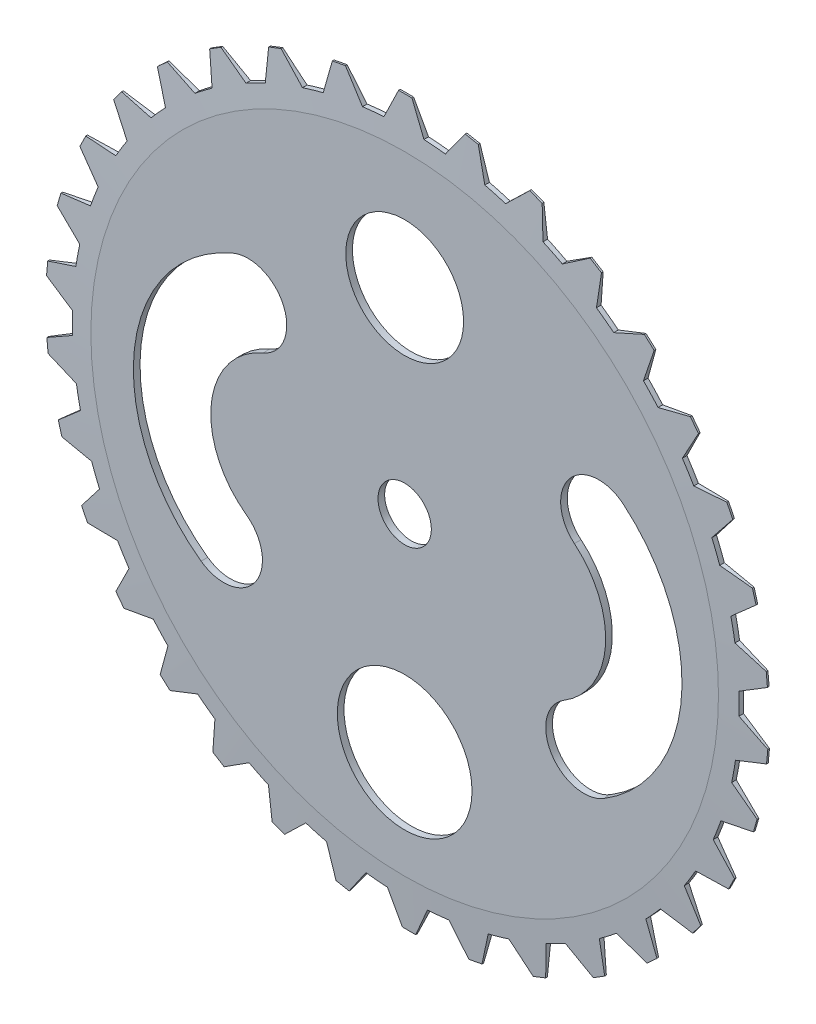
SolidWorks part; units mm, degrees
ref_plane "Front Plane" through (0, 0, 0) normal (0, 0, 1) x (1, 0, 0)
ref_plane "Top Plane" through (0, 0, 0) normal (0, 1, 0) x (1, 0, 0)
ref_plane "Right Plane" through (0, 0, 0) normal (1, 0, 0) x (0, 0, -1)
sketch "Sketch1" plane through (0, 0, 0) normal (0, 0, 1) x (1, 0, 0)
  circle A0 centre (0, 0) radius 63.5
  dimension "D1" = 127
extrude "Boss-Extrude1" add sketch "Sketch1" along normal blind 1.27 contours A0
sketch "Sketch2" plane through (0, 0, 1.27) normal (0, 0, 1) x (1, 0, 0)
  circle A0 centre (0, 0) radius 5.08
  dimension "D1" = 10.16
sketch "Sketch3" plane through (0, 0, 1.27) normal (0, 0, 1) x (1, 0, 0)
  circle A0 centre (0, 37.3308) radius 11.2182
  circle A1 centre (0, -39.311) radius 12.8285
  arc A2 (-29.8323, 19.8682) -> (-34.4638, -21.1959) centre (-20.5919, -1.9673) ccw construction
  arc A3 (-32.7056, 26.6578) -> (-38.7772, -27.175) centre (-20.5919, -1.9673) ccw
  arc A4 (-26.9591, 13.0785) -> (-30.1504, -15.2169) centre (-20.5919, -1.9673) ccw
  arc A5 (-26.9591, 13.0785) -> (-32.7056, 26.6578) centre (-29.8323, 19.8682) ccw
  arc A6 (-38.7772, -27.175) -> (-30.1504, -15.2169) centre (-34.4638, -21.1959) ccw
  arc A7 (36.9799, 16.8548) -> (34.1411, -21.7716) centre (21.7432, -1.4429) cw construction
  arc A8 (37.9274, -27.9799) -> (41.6332, 22.4428) centre (21.7432, -1.4429) ccw
  arc A9 (30.3548, -15.5633) -> (32.3267, 11.2667) centre (21.7432, -1.4429) ccw
  arc A10 (30.3548, -15.5633) -> (37.9274, -27.9799) centre (34.1411, -21.7716) ccw
  arc A11 (41.6332, 22.4428) -> (32.3267, 11.2667) centre (36.9799, 16.8548) ccw
  point P7 (-44.1527, 0.6901)
  point P12 (45.4901, -3.1882)
extrude "Cut-Extrude3" cut sketch "Sketch3" against normal blind 1.27
extrude "Cut-Extrude4" cut sketch "Sketch2" against normal blind 1.27
sketch "Sketch4" plane through (0, 0, 1.27) normal (0, 0, 1) x (1, 0, 0)
  line L0 (-4.1419, 63.3648) -> (3.4781, 63.4047)
  line L1 (-0.3573, 68.8319) -> (0.9127, 68.8319)
  line L2 (0.9127, 68.8319) -> (3.4781, 63.4047)
  line L3 (7.5719, 63.0469) -> (11.0482, 67.9589)
  line L4 (-4.1419, 63.3648) -> (-1.6273, 68.8319)
  line L5 (-1.6273, 68.8319) -> (-0.3573, 68.8319)
  line L6 (11.0482, 67.9589) -> (12.2966, 67.7255)
  line L7 (12.2966, 67.7255) -> (13.545, 67.4922)
  line L8 (13.545, 67.4922) -> (15.0695, 61.686)
  line L9 (7.5719, 63.0469) -> (15.0695, 61.686)
  line L10 (19.0278, 60.5821) -> (23.3475, 64.7717)
  line L11 (23.3475, 64.7717) -> (24.5318, 64.3129)
  line L12 (24.5318, 64.3129) -> (25.716, 63.8541)
  line L13 (25.716, 63.8541) -> (26.1477, 57.8667)
  line L14 (19.0278, 60.5821) -> (26.1477, 57.8667)
  line L15 (29.8358, 56.0542) -> (34.8517, 59.3787)
  line L16 (34.8517, 59.3787) -> (35.9315, 58.7101)
  line L17 (35.9315, 58.7101) -> (37.0113, 58.0416)
  line L18 (37.0113, 58.0416) -> (36.3354, 52.0767)
  line L19 (29.8358, 56.0542) -> (36.3354, 52.0767)
  line L20 (39.6277, 49.6175) -> (45.1691, 51.9637)
  line L21 (45.1691, 51.9637) -> (46.1077, 51.1081)
  line L22 (46.1077, 51.1081) -> (47.0462, 50.2525)
  line L23 (47.0462, 50.2525) -> (45.2858, 44.5134)
  line L24 (39.6277, 49.6175) -> (45.2858, 44.5134)
  line L25 (48.0701, 41.4911) -> (53.9483, 42.7791)
  line L26 (53.9483, 42.7791) -> (54.7137, 41.7656)
  line L27 (54.7137, 41.7656) -> (55.479, 40.7521)
  line L28 (55.479, 40.7521) -> (52.6941, 35.4343)
  line L29 (48.0701, 41.4911) -> (52.6941, 35.4343)
  line L30 (54.8756, 31.9518) -> (60.8904, 32.1377)
  line L31 (60.8904, 32.1377) -> (61.4565, 31.0008)
  line L32 (61.4565, 31.0008) -> (62.0226, 29.864)
  line L33 (62.0226, 29.864) -> (58.3079, 25.1484)
  line L34 (54.8756, 31.9518) -> (58.3079, 25.1484)
  line L35 (59.8124, 21.3244) -> (65.7589, 20.4019)
  line L36 (65.7589, 20.4019) -> (66.1065, 19.1804)
  line L37 (66.1065, 19.1804) -> (66.454, 17.9589)
  line L38 (66.454, 17.9589) -> (61.9361, 14.0062)
  line L39 (59.8124, 21.3244) -> (61.9361, 14.0062)
  line L40 (62.7123, 9.9708) -> (68.3881, 7.9714)
  line L41 (68.3881, 7.9714) -> (68.5053, 6.7068)
  line L42 (68.5053, 6.7068) -> (68.6225, 5.4422)
  line L43 (68.6225, 5.4422) -> (63.4551, 2.387)
  line L44 (62.7123, 9.9708) -> (63.4551, 2.387)
  line L45 (63.4766, -1.7223) -> (68.6884, -4.7306)
  line L46 (68.6884, -4.7306) -> (68.5712, -5.9952)
  line L47 (68.5712, -5.9952) -> (68.454, -7.2598)
  line L48 (68.454, -7.2598) -> (62.8133, -9.3135)
  line L49 (63.4766, -1.7223) -> (62.8133, -9.3135)
  line L50 (62.0793, -13.3568) -> (66.6496, -17.2715)
  line L51 (66.6496, -17.2715) -> (66.302, -18.4931)
  line L52 (66.302, -18.4931) -> (65.9545, -19.7146)
  line L53 (65.9545, -19.7146) -> (60.0324, -20.6969)
  line L54 (62.0793, -13.3568) -> (60.0324, -20.6969)
  line L55 (58.568, -24.5364) -> (62.3411, -29.2243)
  line L56 (62.3411, -29.2243) -> (61.775, -30.3612)
  line L57 (61.775, -30.3612) -> (61.2089, -31.498)
  line L58 (61.2089, -31.498) -> (55.2072, -31.3754)
  line L59 (58.568, -24.5364) -> (55.2072, -31.3754)
  line L60 (53.0622, -34.8805) -> (55.9097, -40.1818)
  line L61 (55.9097, -40.1818) -> (55.1443, -41.1953)
  line L62 (55.1443, -41.1953) -> (54.379, -42.2088)
  line L63 (54.379, -42.2088) -> (48.502, -40.9854)
  line L64 (53.0622, -34.8805) -> (48.502, -40.9854)
  line L65 (45.7495, -44.0368) -> (47.5743, -49.7711)
  line L66 (47.5743, -49.7711) -> (46.6358, -50.6266)
  line L67 (46.6358, -50.6266) -> (45.6972, -51.4822)
  line L68 (45.6972, -51.4822) -> (40.1451, -49.1998)
  line L69 (45.7495, -44.0368) -> (40.1451, -49.1998)
  line L70 (36.8788, -51.6934) -> (37.6189, -57.6654)
  line L71 (37.6189, -57.6654) -> (36.5391, -58.3339)
  line L72 (36.5391, -58.3339) -> (35.4593, -59.0025)
  line L73 (35.4593, -59.0025) -> (30.4211, -55.7387)
  line L74 (36.8788, -51.6934) -> (30.4211, -55.7387)
  line L75 (26.7522, -57.5897) -> (26.3824, -63.596)
  line L76 (26.3824, -63.596) -> (25.1981, -64.0547)
  line L77 (25.1981, -64.0547) -> (24.0139, -64.5135)
  line L78 (24.0139, -64.5135) -> (19.6612, -60.3795)
  line L79 (26.7522, -57.5897) -> (19.6612, -60.3795)
  line L80 (15.7146, -61.5248) -> (14.2474, -67.3609)
  line L81 (14.2474, -67.3609) -> (12.999, -67.5942)
  line L82 (12.999, -67.5942) -> (11.7507, -67.8276)
  line L83 (11.7507, -67.8276) -> (8.2317, -62.9642)
  line L84 (15.7146, -61.5248) -> (8.2317, -62.9642)
  line L85 (4.1419, -63.3648) -> (1.6273, -68.8319)
  line L86 (1.6273, -68.8319) -> (0.3573, -68.8319)
  line L87 (0.3573, -68.8319) -> (-0.9127, -68.8319)
  line L88 (-0.9127, -68.8319) -> (-3.4781, -63.4047)
  line L89 (4.1419, -63.3648) -> (-3.4781, -63.4047)
  line L90 (-7.5719, -63.0469) -> (-11.0482, -67.9589)
  line L91 (-11.0482, -67.9589) -> (-12.2966, -67.7255)
  line L92 (-12.2966, -67.7255) -> (-13.545, -67.4922)
  line L93 (-13.545, -67.4922) -> (-15.0695, -61.686)
  line L94 (-7.5719, -63.0469) -> (-15.0695, -61.686)
  line L95 (-19.0278, -60.5821) -> (-23.3475, -64.7717)
  line L96 (-23.3475, -64.7717) -> (-24.5318, -64.3129)
  line L97 (-24.5318, -64.3129) -> (-25.716, -63.8541)
  line L98 (-25.716, -63.8541) -> (-26.1477, -57.8667)
  line L99 (-19.0278, -60.5821) -> (-26.1477, -57.8667)
  line L100 (-29.8358, -56.0542) -> (-34.8517, -59.3787)
  line L101 (-34.8517, -59.3787) -> (-35.9315, -58.7101)
  line L102 (-35.9315, -58.7101) -> (-37.0113, -58.0416)
  line L103 (-37.0113, -58.0416) -> (-36.3354, -52.0767)
  line L104 (-29.8358, -56.0542) -> (-36.3354, -52.0767)
  line L105 (-39.6277, -49.6175) -> (-45.1691, -51.9637)
  line L106 (-45.1691, -51.9637) -> (-46.1077, -51.1081)
  line L107 (-46.1077, -51.1081) -> (-47.0462, -50.2525)
  line L108 (-47.0462, -50.2525) -> (-45.2858, -44.5134)
  line L109 (-39.6277, -49.6175) -> (-45.2858, -44.5134)
  line L110 (-48.0701, -41.4911) -> (-53.9483, -42.7791)
  line L111 (-53.9483, -42.7791) -> (-54.7137, -41.7656)
  line L112 (-54.7137, -41.7656) -> (-55.479, -40.7521)
  line L113 (-55.479, -40.7521) -> (-52.6941, -35.4343)
  line L114 (-48.0701, -41.4911) -> (-52.6941, -35.4343)
  line L115 (-54.8756, -31.9518) -> (-60.8904, -32.1377)
  line L116 (-60.8904, -32.1377) -> (-61.4565, -31.0008)
  line L117 (-61.4565, -31.0008) -> (-62.0226, -29.864)
  line L118 (-62.0226, -29.864) -> (-58.3079, -25.1484)
  line L119 (-54.8756, -31.9518) -> (-58.3079, -25.1484)
  line L120 (-59.8124, -21.3244) -> (-65.7589, -20.4019)
  line L121 (-65.7589, -20.4019) -> (-66.1065, -19.1804)
  line L122 (-66.1065, -19.1804) -> (-66.454, -17.9589)
  line L123 (-66.454, -17.9589) -> (-61.9361, -14.0062)
  line L124 (-59.8124, -21.3244) -> (-61.9361, -14.0062)
  line L125 (-62.7123, -9.9708) -> (-68.3881, -7.9714)
  line L126 (-68.3881, -7.9714) -> (-68.5053, -6.7068)
  line L127 (-68.5053, -6.7068) -> (-68.6225, -5.4422)
  line L128 (-68.6225, -5.4422) -> (-63.4551, -2.387)
  line L129 (-62.7123, -9.9708) -> (-63.4551, -2.387)
  line L130 (-63.4766, 1.7223) -> (-68.6884, 4.7306)
  line L131 (-68.6884, 4.7306) -> (-68.5712, 5.9952)
  line L132 (-68.5712, 5.9952) -> (-68.454, 7.2598)
  line L133 (-68.454, 7.2598) -> (-62.8133, 9.3135)
  line L134 (-63.4766, 1.7223) -> (-62.8133, 9.3135)
  line L135 (-62.0793, 13.3568) -> (-66.6496, 17.2715)
  line L136 (-66.6496, 17.2715) -> (-66.302, 18.4931)
  line L137 (-66.302, 18.4931) -> (-65.9545, 19.7146)
  line L138 (-65.9545, 19.7146) -> (-60.0324, 20.6969)
  line L139 (-62.0793, 13.3568) -> (-60.0324, 20.6969)
  line L140 (-58.568, 24.5364) -> (-62.3411, 29.2243)
  line L141 (-62.3411, 29.2243) -> (-61.775, 30.3612)
  line L142 (-61.775, 30.3612) -> (-61.2089, 31.498)
  line L143 (-61.2089, 31.498) -> (-55.2072, 31.3754)
  line L144 (-58.568, 24.5364) -> (-55.2072, 31.3754)
  line L145 (-53.0622, 34.8805) -> (-55.9097, 40.1818)
  line L146 (-55.9097, 40.1818) -> (-55.1443, 41.1953)
  line L147 (-55.1443, 41.1953) -> (-54.379, 42.2088)
  line L148 (-54.379, 42.2088) -> (-48.502, 40.9854)
  line L149 (-53.0622, 34.8805) -> (-48.502, 40.9854)
  line L150 (-45.7495, 44.0368) -> (-47.5743, 49.7711)
  line L151 (-47.5743, 49.7711) -> (-46.6358, 50.6266)
  line L152 (-46.6358, 50.6266) -> (-45.6972, 51.4822)
  line L153 (-45.6972, 51.4822) -> (-40.1451, 49.1998)
  line L154 (-45.7495, 44.0368) -> (-40.1451, 49.1998)
  line L155 (-36.8788, 51.6934) -> (-37.6189, 57.6654)
  line L156 (-37.6189, 57.6654) -> (-36.5391, 58.3339)
  line L157 (-36.5391, 58.3339) -> (-35.4593, 59.0025)
  line L158 (-35.4593, 59.0025) -> (-30.4211, 55.7387)
  line L159 (-36.8788, 51.6934) -> (-30.4211, 55.7387)
  line L160 (-26.7522, 57.5897) -> (-26.3824, 63.596)
  line L161 (-26.3824, 63.596) -> (-25.1981, 64.0547)
  line L162 (-25.1981, 64.0547) -> (-24.0139, 64.5135)
  line L163 (-24.0139, 64.5135) -> (-19.6612, 60.3795)
  line L164 (-26.7522, 57.5897) -> (-19.6612, 60.3795)
  line L165 (-15.7146, 61.5248) -> (-14.2474, 67.3609)
  line L166 (-14.2474, 67.3609) -> (-12.999, 67.5942)
  line L167 (-12.999, 67.5942) -> (-11.7507, 67.8276)
  line L168 (-11.7507, 67.8276) -> (-8.2317, 62.9642)
  line L169 (-15.7146, 61.5248) -> (-8.2317, 62.9642)
  circle A0 centre (0, 0) radius 63.5 construction
  point P177 (0, 0)
  dimension "D1" = 1.27
  dimension "D2" = 1.27
  dimension "D3" = 65
  dimension "D4" = 7.62
  dimension "D5" = 65
  dimension "D6" = 0.3
  dimension "D7" = 34
extrude "Boss-Extrude2" add sketch "Sketch4" against normal blind 1.27
sketch "Sketch6" plane through (0, 0, 1.27) normal (0, 0, 1) x (1, 0, 0)
  circle A0 centre (0, 0) radius 59.7715
extrude "Cut-Extrude7" cut sketch "Sketch6" against normal blind 1.27 draft 87 flip side to cut
ref_plane "Plane1" through (0, 0, 0.635) normal (0, 0, 1) x (1, 0, 0)
mirror "Mirror1" about plane through (0, 0, 0.635) normal (0, 0, 1) of "Cut-Extrude7"
